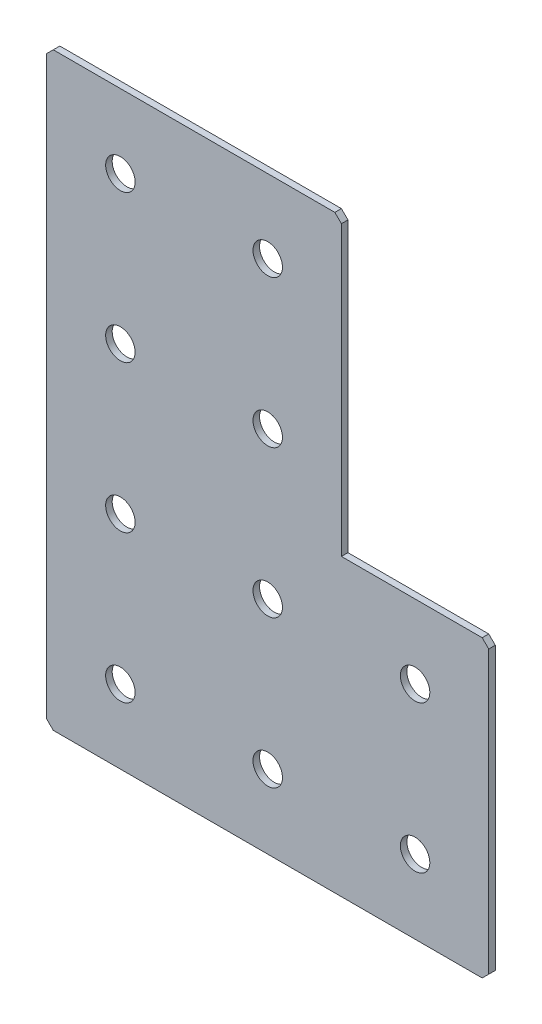
SolidWorks part; units mm, degrees
material "Простая углеродистая сталь"
ref_plane "Спереди(Плоскость XY)" through (0, 0, 0) normal (0, 0, 1) x (1, 0, 0)
ref_plane "Сверху(Плоскость XZ)" through (0, 0, 0) normal (0, 1, 0) x (1, 0, 0)
ref_plane "Справа(Плоскость ZY)" through (0, 0, 0) normal (1, 0, 0) x (0, 0, -1)
sketch "Эскиз1" plane through (0, 0, 0) normal (0, 0, -1) x (1, 0, 0)
  line L0 (0, 0) -> (0, 180)
  line L1 (0, 180) -> (135, 180)
  line L2 (135, 180) -> (135, 90)
  line L3 (135, 90) -> (90, 90)
  line L4 (90, 90) -> (90, 0)
  line L5 (90, 0) -> (0, 0)
  line L6 (135, 90) -> (90, 0) construction
  dimension "D1" = 180
  dimension "D2" = 90
  dimension "D3" = 90
  dimension "D4" = 135
extrude "Бобышка-Вытянуть1" add sketch "Эскиз1" along normal blind 2
hole_wizard "Отверстие с зазором M81" positions "Эскиз2" profile "Эскиз3" hole size "M8" standard "DIN" end condition through all
sketch "Эскиз2" plane through (0, 0, -2) normal (0, 0, -1) x (1, 0, 0)
  line L0 (22.5, 0) -> (22.5, 180) construction
  line L1 (0, 0) -> (90, 0) construction
  line L2 (135, 180) -> (0, 180) construction
  line L3 (0, 180) -> (0, 0) construction
  line L4 (0, 0) -> (90, 0) construction
  point P0 (22.5, 157.5)
  point P2 (22.5, 112.5)
  point P4 (22.5, 67.5)
  point P6 (22.5, 22.5)
  point P27 (67.5, 157.5)
  point P29 (67.5, 112.5)
  point P35 (67.5, 67.5)
  point P37 (67.5, 22.5)
  point P39 (112.5, 157.5)
  point P41 (112.5, 112.5)
  dimension "D1" = 45
  dimension "D2" = 45
  dimension "D3" = 45
  dimension "D4" = 22.5
  dimension "D5" = 45
  dimension "D6" = 22.5
  dimension "D7" = 45
sketch "Эскиз3" plane through (22.5, -157.5, -2) normal (1, 0, 0) x (0, 1, 0)
  line L0 (0, 0) -> (0, 2)
  line L1 (0, 2) -> (4.5, 2)
  line L2 (4.5, 2) -> (4.5, 0)
  line L5 (4.5, 0) -> (0, 0)
  line L11 (0, -6.35) -> (0, 107.95) construction
  dimension "Диаметр сквозного отверстия" = 9
  dimension "Глубина сквозного отверстия" = 2
chamfer "Фаска1" distance 2 angle 45 5 edges at (0, 0, -1) (90, 0, -1) (135, -90, -1) (135, -180, -1) (0, -180, -1)
